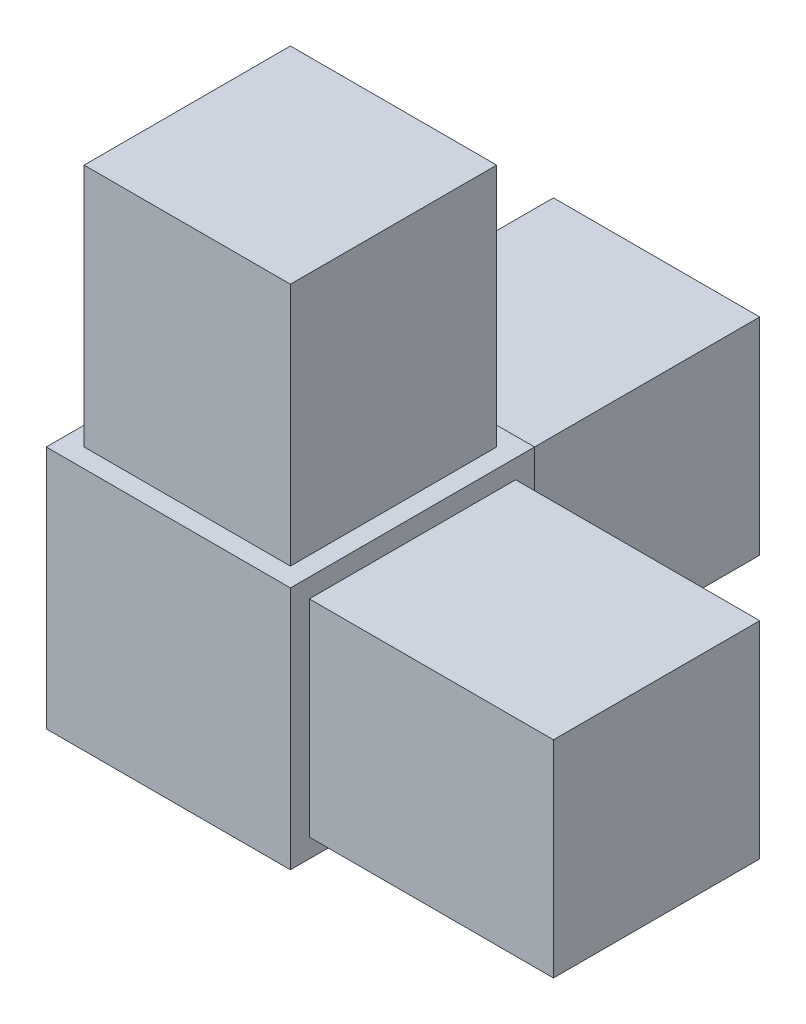
SolidWorks part; units mm, degrees
ref_plane "Front Plane" through (0, 0, 0) normal (0, 0, 1) x (1, 0, 0)
ref_plane "Top Plane" through (0, 0, 0) normal (0, 1, 0) x (1, 0, 0)
ref_plane "Right Plane" through (0, 0, 0) normal (1, 0, 0) x (0, 0, -1)
sketch "Sketch1" plane through (0, 0, 0) normal (0, 1, 0) x (1, 0, 0)
  line L1 (-10, -10) -> (10, -10)
  line L2 (-10, -10) -> (-10, 10)
  line L3 (-10, 10) -> (10, 10)
  line L4 (10, -10) -> (10, 10)
  line L5 (-10, -10) -> (10, 10) construction
  line L6 (-10, 10) -> (10, -10) construction
  point P0 (0, 0)
  dimension "D1" = 20
extrude "Boss-Extrude1" add sketch "Sketch1" along normal blind 20 contours L3 L4 L1 L2
sketch "Sketch2" plane through (0, 20, 0) normal (0, 1, 0) x (1, 0, 0)
  line L8 (-8.45, -8.45) -> (8.45, -8.45)
  line L9 (8.45, -8.45) -> (8.45, 8.45)
  line L10 (-8.45, 8.45) -> (-8.45, -8.45)
  line L11 (8.45, 8.45) -> (-8.45, 8.45)
  line L12 (-8.45, -8.45) -> (8.45, -8.45)
  line L13 (8.45, -8.45) -> (8.45, 8.45)
  line L14 (-8.45, 8.45) -> (-8.45, -8.45)
  line L15 (8.45, 8.45) -> (-8.45, 8.45)
  dimension "D1" = 1.55
sketch "Sketch3" plane through (10, 0, 0) normal (1, 0, 0) x (0, 0, -1)
  line L8 (-8.45, 1.55) -> (8.45, 1.55)
  line L9 (8.45, 1.55) -> (8.45, 18.45)
  line L10 (-8.45, 18.45) -> (-8.45, 1.55)
  line L11 (8.45, 18.45) -> (-8.45, 18.45)
  line L12 (-8.45, 1.55) -> (8.45, 1.55)
  line L13 (8.45, 1.55) -> (8.45, 18.45)
  line L14 (-8.45, 18.45) -> (-8.45, 1.55)
  line L15 (8.45, 18.45) -> (-8.45, 18.45)
  dimension "D1" = 1.55
sketch "Sketch4" plane through (0, 0, -10) normal (0, 0, -1) x (-1, 0, 0)
  line L8 (-8.45, 1.55) -> (8.45, 1.55)
  line L9 (8.45, 1.55) -> (8.45, 18.45)
  line L10 (8.45, 18.45) -> (-8.45, 18.45)
  line L11 (-8.45, 18.45) -> (-8.45, 1.55)
  line L12 (-8.45, 1.55) -> (8.45, 1.55)
  line L13 (8.45, 1.55) -> (8.45, 18.45)
  line L14 (8.45, 18.45) -> (-8.45, 18.45)
  line L15 (-8.45, 18.45) -> (-8.45, 1.55)
  dimension "D1" = 1.55
extrude "Boss-Extrude2" add sketch "Sketch2" along normal blind 20
extrude "Boss-Extrude3" add sketch "Sketch3" along normal blind 20
extrude "Boss-Extrude4" add sketch "Sketch4" along normal blind 20
